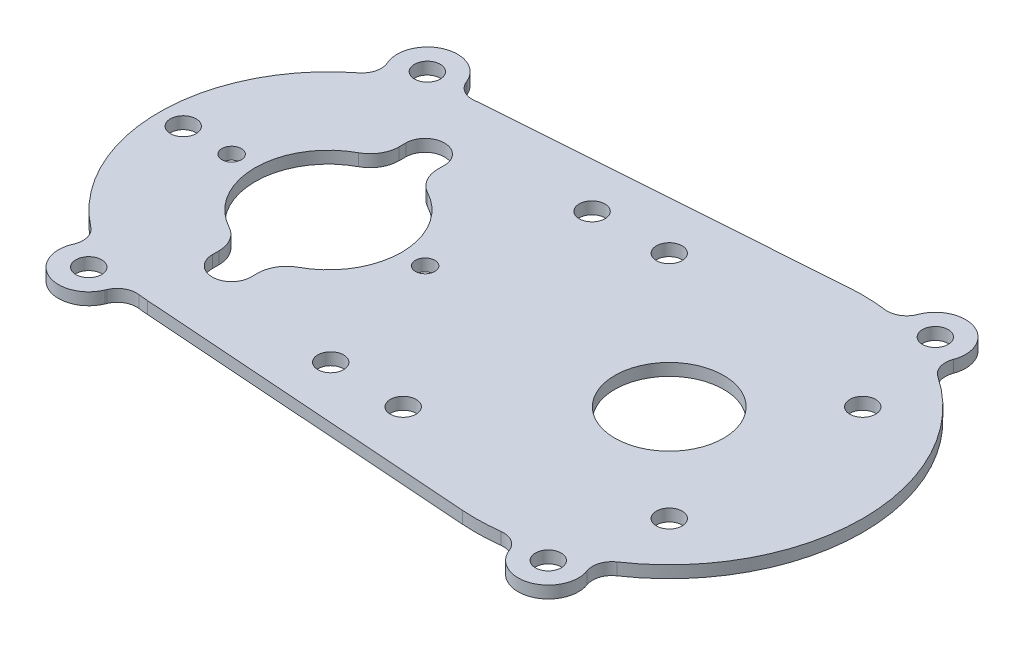
SolidWorks part; units mm, degrees
material "6061 Alloy"
ref_plane "Front Plane" through (0, 0, 0) normal (0, 0, 1) x (1, 0, 0)
ref_plane "Top Plane" through (0, 0, 0) normal (0, 1, 0) x (1, 0, 0)
ref_plane "Right Plane" through (0, 0, 0) normal (1, 0, 0) x (0, 0, -1)
sketch "Sketch1" plane through (0, 0, 0) normal (0, 1, 0) x (1, 0, 0)
  line L0 (87.0156, 23.109) -> (-1.4599, 13.6381) construction
  line L1 (-25.4, 0) -> (0, -25.4) construction
  line L2 (-25.4, 0) -> (0, 25.4) construction
  line L3 (0, 25.4) -> (25.4, 0) construction
  line L4 (0, -25.4) -> (25.4, 0) construction
  line L5 (-25.4, 0) -> (25.4, 0) construction
  line L6 (0, 25.4) -> (0, -25.4) construction
  line L7 (87.0156, -23.109) -> (-1.4599, -13.6381) construction
  line L8 (85.8846, 50.6719) -> (-3.1541, 44.338)
  line L9 (85.8846, -50.6719) -> (-3.1541, -44.338)
  line L10 (0, 0) -> (89.4893, 0) construction
  circle A1 centre (0, 0) radius 13.716 construction
  circle A2 centre (89.4893, 0) radius 23.241 construction
  circle A3 centre (89.4893, 0) radius 14.2812
  circle A4 centre (0, 0) radius 19.2405
  arc A5 (-3.1541, 44.338) -> (-3.1541, -44.338) centre (0, 0) ccw
  arc A6 (85.8846, 50.6719) -> (85.8846, -50.6719) centre (89.4893, 0) cw
  point P0 (0, 0)
  point P2 (140.2893, 0)
  point P27 (-44.45, 0)
  dimension "D1" = 50.8
  dimension "D2" = 27.432
  dimension "D3" = 46.482
  dimension "D5" = 28.5623
  dimension "D6" = 38.481
  dimension "D4" = 89.4893
  dimension "D7" = 44.45
  dimension "D8" = 50.8
extrude "Boss-Extrude1" add sketch "Sketch1" along normal blind 3.175
hole_wizard "#10 Clearance Hole1" positions "Sketch2" profile "Sketch3" hole size "#10" standard "ANSI Inch" end condition through all
sketch "Sketch2" plane through (0, 3.175, 0) normal (0, 1, 0) x (1, 0, 0)
  line L0 (-44.45, 0) -> (-19.2405, 0) construction
  arc A0 (-3.1541, 44.338) -> (-3.1541, -44.338) centre (0, 0) ccw construction
  circle A1 centre (0, 0) radius 19.2405 construction
  point P0 (0, 25.4)
  point P3 (25.4, 0)
  point P6 (0, -25.4)
  point P9 (-25.4, 0)
sketch "Sketch3" plane through (0, 3.175, -25.4) normal (1, 0, 0) x (0, 0, 1)
  line L0 (0, 0) -> (0, 3.175)
  line L1 (0, 3.175) -> (2.5527, 3.175)
  line L2 (2.5527, 3.175) -> (2.5527, 0)
  line L5 (2.5527, 0) -> (0, 0)
  line L11 (0, -6.35) -> (0, 107.95) construction
  dimension "Thru Hole Dia." = 5.1054
  dimension "Thru Hole Depth" = 3.175
hole_wizard "1/4 Clearance Hole1" positions "Sketch4" profile "Sketch5" hole size "1/4" standard "ANSI Inch" end condition through all
sketch "Sketch4" plane through (0, 3.175, 0) normal (0, 1, 0) x (1, 0, 0)
  line L0 (-31.8452, 0) -> (126.5098, 0) construction
  line L1 (140.2893, 0) -> (112.7303, 0) construction
  line L2 (-19.2405, 0) -> (-44.45, 0) construction
  line L3 (-3.1541, -44.338) -> (85.8846, -50.6719) construction
  arc A0 (85.8846, -50.6719) -> (85.8846, 50.6719) centre (89.4893, 0) ccw construction
  circle A1 centre (89.4893, 0) radius 23.241 construction
  circle A2 centre (0, 0) radius 19.2405 construction
  arc A3 (-3.1541, 44.338) -> (-3.1541, -44.338) centre (0, 0) ccw construction
  circle A5 centre (89.4893, 0) radius 14.2812 construction
  point P4 (54.5643, 34.925)
  point P6 (54.5643, -34.925)
  point P54 (114.8893, 25.4)
  point P56 (114.8893, -25.4)
  point P62 (-38.1, 0)
  point P64 (34.925, -34.3147)
  point P68 (34.925, 34.3147)
  dimension "D1" = 34.925
  dimension "D3" = 25.4
  dimension "D2" = 25.4
  dimension "D4" = 34.925
  dimension "D5" = 38.1
  dimension "D6" = 34.925
  dimension "D7" = 12.7
  dimension "D8" = 34.3147
sketch "Sketch5" plane through (54.5643, 3.175, -34.925) normal (1, 0, 0) x (0, 0, 1)
  line L0 (0, 0) -> (0, 3.175)
  line L1 (0, 3.175) -> (3.3782, 3.175)
  line L2 (3.3782, 3.175) -> (3.3782, 0)
  line L5 (3.3782, 0) -> (0, 0)
  line L11 (0, -6.35) -> (0, 107.95) construction
  dimension "Thru Hole Dia." = 6.7564
  dimension "Thru Hole Depth" = 3.175
sketch "Sketch6" plane through (0, 3.175, 0) normal (0, 1, 0) x (1, 0, 0)
  line L0 (5.08, 25.4) -> (5.08, 18.5578)
  line L1 (-5.08, 25.4) -> (-5.08, 18.5578)
  line L2 (-25.4, 0) -> (25.4, 0) construction
  line L3 (5.08, -25.4) -> (5.08, -18.5578)
  line L4 (-5.08, -25.4) -> (-5.08, -18.5578)
  arc A0 (-5.08, 25.4) -> (5.08, 25.4) centre (0, 25.4) cw
  circle A1 centre (0, 0) radius 19.2405 construction
  arc A2 (-5.08, 18.5578) -> (5.08, 18.5578) centre (0, 0) cw
  arc A3 (-5.08, -25.4) -> (5.08, -25.4) centre (0, -25.4) ccw
  arc A4 (-5.08, -18.5578) -> (5.08, -18.5578) centre (0, 0) ccw
  circle M7 centre (0, 25.4) radius 2.5527
  circle M9 centre (0, -25.4) radius 2.5527
  circle M16 centre (0, 0) radius 19.2405
  dimension "D1" = 5.08
extrude "Cut-Extrude1" cut sketch "Sketch6" against normal through all contours A0 L1 L0 M16 M7 | L4 A3 L3 M16 M9
fillet "Fillet1" radius 7.62 4 edges at (-5.08, 1.5875, -18.5578) (5.08, 1.5875, -18.5578) (-5.08, 1.5875, 18.5578) (5.08, 1.5875, 18.5578)
sketch "Sketch7" plane through (0, 3.175, 0) normal (0, 1, 0) x (1, 0, 0)
  line L0 (-3.1541, -44.338) -> (85.8846, -50.6719) construction
  line L1 (85.8846, 50.6719) -> (-3.1541, 44.338) construction
  line L2 (-3.1541, -44.338) -> (85.8846, -50.6719)
  line L3 (85.8846, 50.6719) -> (-3.1541, 44.338)
  line L4 (83.1811, 88.6759) -> (-5.8576, 82.3419)
  line L5 (-5.8576, -82.3419) -> (83.1811, -88.6759)
  arc A0 (85.8846, -50.6719) -> (85.8846, 50.6719) centre (89.4893, 0) ccw construction
  arc A1 (-3.1541, 44.338) -> (-3.1541, -44.338) centre (0, 0) ccw construction
  arc A2 (85.8846, -50.6719) -> (85.8846, 50.6719) centre (89.4893, 0) ccw
  arc A3 (-3.1541, 44.338) -> (-3.1541, -44.338) centre (0, 0) ccw
  arc A4 (-5.8576, 82.3419) -> (-5.8576, -82.3419) centre (0, 0) ccw
  arc A5 (83.1811, -88.6759) -> (83.1811, 88.6759) centre (89.4893, 0) ccw
  dimension "D1" = 38.1
extrude "Boss-Extrude2" [suppressed] add sketch "Sketch7" against normal up to surface (6.35 mm away)
sketch "Sketch8" plane through (0, 3.175, 0) normal (0, 1, 0) x (1, 0, 0)
  line L0 (0, 0) -> (89.4893, 0) construction
  line L1 (114.5394, -44.1943) -> (115.9714, -48.013)
  line L2 (108.5393, -50.8) -> (89.4893, 0) construction
  line L3 (99.6752, -49.7683) -> (101.1072, -53.587)
  line L4 (99.6752, 49.7683) -> (101.1072, 53.587)
  line L5 (114.5394, 44.1943) -> (115.9714, 48.013)
  line L6 (-9.4444, -43.4351) -> (-11.1303, -47.4944)
  line L7 (-18.4607, -44.45) -> (0, 0) construction
  line L8 (-24.1053, -37.3462) -> (-25.7912, -41.4056)
  line L9 (-9.4444, 43.4351) -> (-11.1303, 47.4944)
  line L10 (-24.1053, 37.3462) -> (-25.7912, 41.4056)
  circle A0 centre (108.5393, -50.8) radius 3.429 construction
  circle A1 centre (-18.4607, -44.45) radius 3.429 construction
  circle A2 centre (-18.4607, 44.45) radius 3.429 construction
  circle A3 centre (108.5393, 50.8) radius 3.429 construction
  circle A4 centre (89.4893, 0) radius 14.2812 construction
  arc A5 (85.8846, -50.6719) -> (85.8846, 50.6719) centre (89.4893, 0) ccw construction
  arc A6 (115.9714, -48.013) -> (101.1072, -53.587) centre (108.5393, -50.8) cw
  arc A7 (114.5394, -44.1943) -> (99.6752, -49.7683) centre (89.4893, 0) cw
  arc A8 (115.9714, 48.013) -> (101.1072, 53.587) centre (108.5393, 50.8) ccw
  arc A9 (114.5394, 44.1943) -> (99.6752, 49.7683) centre (89.4893, 0) ccw
  arc A10 (-3.1541, 44.338) -> (-3.1541, -44.338) centre (0, 0) ccw construction
  arc A11 (-11.1303, -47.4944) -> (-25.7912, -41.4056) centre (-18.4607, -44.45) cw
  arc A12 (-9.4444, -43.4351) -> (-24.1053, -37.3462) centre (0, 0) cw
  arc A13 (-9.4444, 43.4351) -> (-24.1053, 37.3462) centre (0, 0) ccw
  arc A14 (-11.1303, 47.4944) -> (-25.7912, 41.4056) centre (-18.4607, 44.45) ccw
  dimension "D1" = 6.858
  dimension "D2" = 19.05
  dimension "D3" = 50.8
  dimension "D4" = 44.45
  dimension "D5" = 107.95
  dimension "D6" = 7.9375
  dimension "D7" = 7.9375
extrude "Boss-Extrude3" add sketch "Sketch8" against normal up to surface (3.175 mm away) up to face at (54.5643, 0, -31.5468)
fillet "Fillet2" radius 5.08 8 edges at (99.6752, 1.5875, -49.7683) (114.5394, 1.5875, -44.1943) (-9.4444, 1.5875, -43.4351) (-24.1053, 1.5875, -37.3462) (-24.1053, 1.5875, 37.3462) (-9.4444, 1.5875, 43.4351) (114.5394, 1.5875, 44.1943) (99.6752, 1.5875, 49.7683)
hole_wizard "1/4 Clearance Hole2" positions "Sketch9" profile "Sketch10" hole size "1/4" standard "ANSI Inch" end condition through all
sketch "Sketch9" plane through (0, 3.175, 0) normal (0, 1, 0) x (1, 0, 0)
  point P0 (108.5393, -50.8)
  point P3 (-18.4607, -44.45)
  point P6 (-18.4607, 44.45)
  point P9 (108.5393, 50.8)
sketch "Sketch10" plane through (108.5393, 3.175, 50.8) normal (1, 0, 0) x (0, 0, 1)
  line L0 (0, 0) -> (0, 3.175)
  line L1 (0, 3.175) -> (3.3782, 3.175)
  line L2 (3.3782, 3.175) -> (3.3782, 0)
  line L5 (3.3782, 0) -> (0, 0)
  line L11 (0, -6.35) -> (0, 107.95) construction
  dimension "Thru Hole Dia." = 6.7564
  dimension "Thru Hole Depth" = 3.175
sketch "Sketch11" [suppressed] plane through (0, 3.175, 0) normal (0, 1, 0) x (1, 0, 0)
  circle A0 centre (89.4893, 0) radius 14.6622
  dimension "D1" = 29.3243
extrude "Cut-Extrude2" [suppressed] cut sketch "Sketch11" against normal through all
